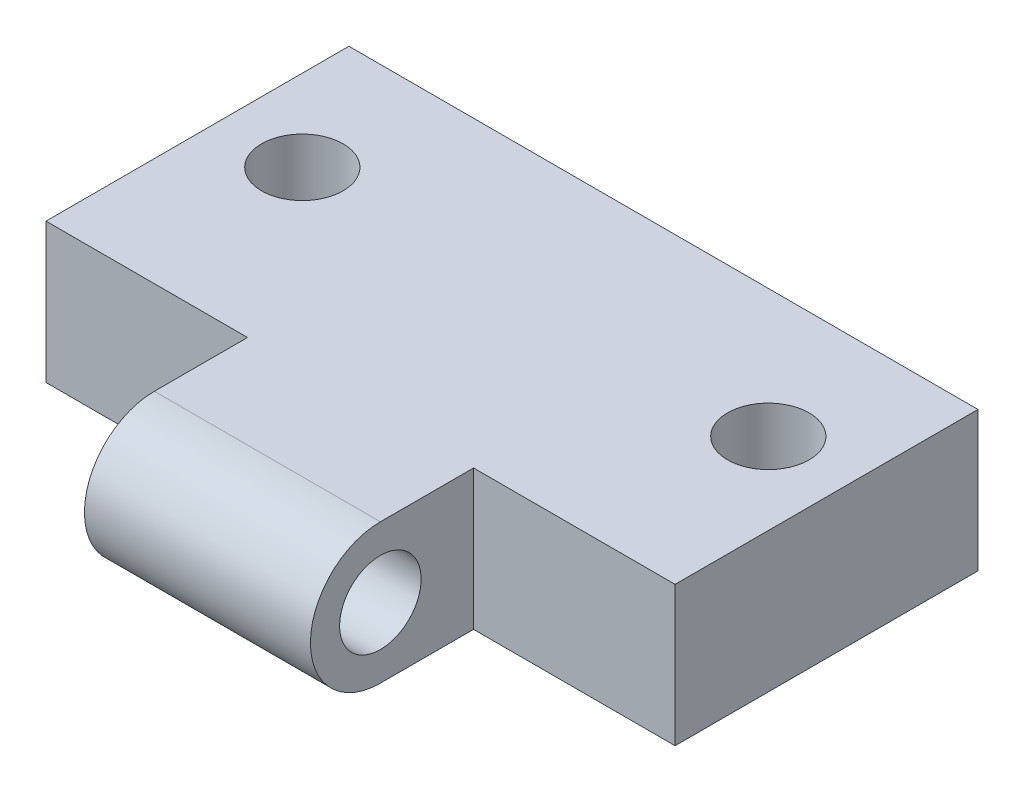
SolidWorks part; units mm, degrees
ref_plane "Front Plane" through (0, 0, 0) normal (0, 0, 1) x (1, 0, 0)
ref_plane "Top Plane" through (0, 0, 0) normal (0, 1, 0) x (1, 0, 0)
ref_plane "Right Plane" through (0, 0, 0) normal (1, 0, 0) x (0, 0, -1)
sketch "Sketch2" plane through (0, 0, 0) normal (1, 0, 0) x (0, 0, -1)
  line L0 (0, -3) -> (17, -3)
  line L1 (17, -3) -> (17, 3)
  line L2 (17, 3) -> (0, 3)
  line L3 (0, 0) -> (0, 3) construction
  line L4 (0, 0) -> (17, 0) construction
  arc A2 (0, 3) -> (0, -3) centre (0, 0) ccw
  circle A3 centre (0, 0) radius 1.75
  dimension "D1" = 3.5
  dimension "D2" = 6
  dimension "D3" = 17
extrude "Boss-Extrude2" add sketch "Sketch2" along normal blind 27
sketch "Sketch3" plane through (0, -3, 0) normal (0, -1, 0) x (1, 0, 0)
  line L0 (3.5, -11.5) -> (23.5, -11.5) construction
  line L1 (13.5, -11.5) -> (13.5, -4) construction
  line L2 (27, -17) -> (0, -17) construction
  line L3 (27, 0) -> (0, 0) construction
  line L5 (8.65, 2) -> (8.65, -4) construction
  line L6 (8.65, -4) -> (18.35, -4) construction
  line L7 (18.35, 4) -> (18.35, -4) construction
  line L11 (18.35, -4) -> (27, -4)
  line L12 (18.35, -4) -> (18.35, 3)
  line L13 (18.35, 3) -> (27, 3)
  line L14 (27, -4) -> (27, 3)
  line L15 (8.65, -4) -> (0, -4)
  line L16 (8.65, -4) -> (8.65, 3)
  line L17 (8.65, 3) -> (0, 3)
  line L18 (0, -4) -> (0, 3)
  circle A0 centre (3.5, -11.5) radius 1.75
  circle A1 centre (23.5, -11.5) radius 1.75
  point P15 (18.35, 0)
  dimension "D1" = 3.5
  dimension "D2" = 3.5
  dimension "D3" = 20
  dimension "D4" = 5.5
  dimension "D5" = 9.7
  dimension "D6" = 7
extrude "Cut-Extrude1" cut sketch "Sketch3" against normal blind 30
sketch "Sketch4" plane through (0, -3, 0) normal (0, -1, 0) x (1, 0, 0)
  circle A0 centre (3.5, -11.5) radius 3
  circle A1 centre (23.5, -11.5) radius 3
  dimension "D1" = 6
extrude "Cut-Extrude2" cut sketch "Sketch4" against normal blind 3
